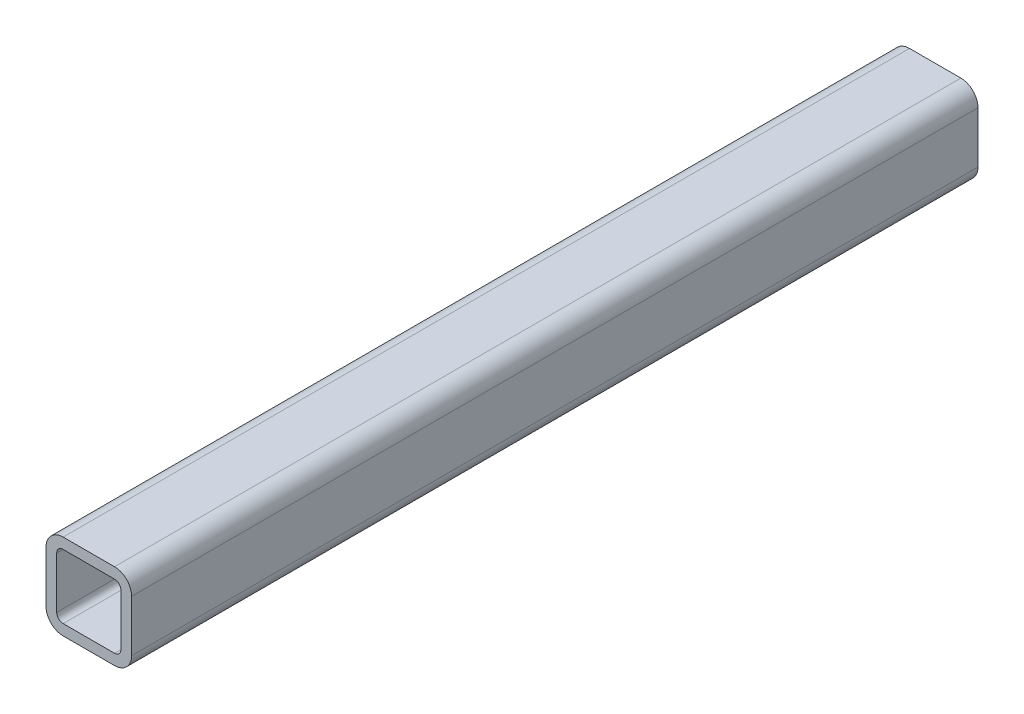
SolidWorks part; units mm, degrees
material "Plain Carbon Steel"
ref_plane "Front" through (0, 0, 0) normal (0, 0, 1) x (1, 0, 0)
ref_plane "Top" through (0, 0, 0) normal (0, 1, 0) x (1, 0, 0)
ref_plane "Right" through (0, 0, 0) normal (1, 0, 0) x (0, 0, -1)
sketch "Sketch1" plane through (0, 0, 0) normal (1, 0, 0) x (0, 0, -1)
  line L0 (0, 0) -> (251.1044, 0)
  dimension "D1" = 251.1044
other "Square tubing 1 X 1 X 0.125(1)"
ref_plane "Plane1" through (0, 0, 0) normal (0, 0, -1) x (0, 1, 0)
sketch "Sketch11" plane through (0, 0, 0) normal (0, 0, -1) x (0, 1, 0)
  line L0 (-7.62, -9.525) -> (7.62, -9.525)
  line L1 (-9.525, -7.62) -> (-9.525, 7.62)
  line L2 (7.62, 9.525) -> (-7.62, 9.525)
  line L3 (9.525, 7.62) -> (9.525, -7.62)
  line L4 (-7.62, -12.7) -> (7.62, -12.7)
  line L5 (-12.7, -7.62) -> (-12.7, 7.62)
  line L6 (7.62, 12.7) -> (-7.62, 12.7)
  line L7 (12.7, 7.62) -> (12.7, -7.62)
  line L8 (0, 0) -> (9.525, 0) construction
  line L9 (0, 0) -> (0, 9.525) construction
  arc A0 (12.7, 7.62) -> (7.62, 12.7) centre (7.62, 7.62) ccw
  arc A1 (7.62, -12.7) -> (12.7, -7.62) centre (7.62, -7.62) ccw
  arc A2 (-12.7, -7.62) -> (-7.62, -12.7) centre (-7.62, -7.62) ccw
  arc A3 (-7.62, 12.7) -> (-12.7, 7.62) centre (-7.62, 7.62) ccw
  arc A4 (-7.62, 9.525) -> (-9.525, 7.62) centre (-7.62, 7.62) ccw
  arc A5 (9.525, 7.62) -> (7.62, 9.525) centre (7.62, 7.62) ccw
  arc A6 (7.62, -9.525) -> (9.525, -7.62) centre (7.62, -7.62) ccw
  arc A7 (-9.525, -7.62) -> (-7.62, -9.525) centre (-7.62, -7.62) ccw
  point P3 (0, 12.7)
  point P4 (12.7, 0)
  point P5 (0, -12.7)
  point P6 (-12.7, 0)
  point P7 (-12.7, 12.7)
  point P8 (-12.7, -12.7)
  point P33 (0, 0)
  point P35 (12.7, -12.7)
  point P36 (12.7, 12.7)
  point P37 (0, 0)
  dimension "D1" = 5.08
  dimension "Thickness" = 3.175
  dimension "V_leg" = 25.4
equation "\"Total Cutting Length\"= \"Cutting Length-Outer\" + \"Cutting Length-Inner\""
equation "\"Amount in ft^2\"= \"Bounding Box Area-Blank\" / 144"
